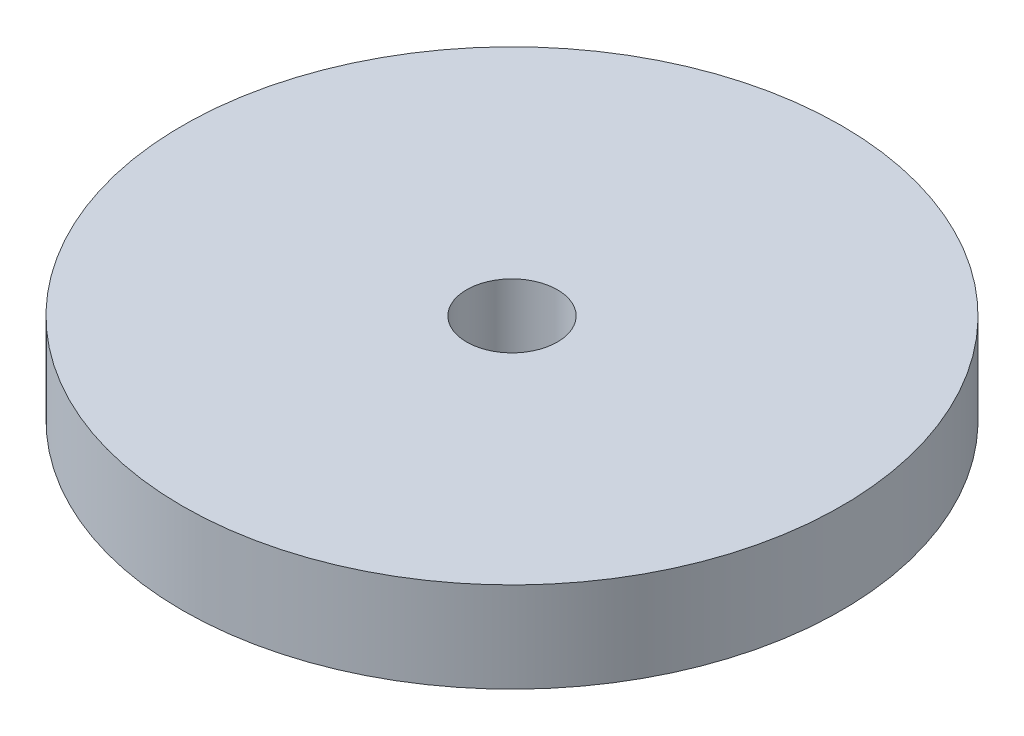
SolidWorks part; units mm, degrees
material "Delrin 2700 NC010, Low Viscosity Acetal Copolymer (SS)"
ref_plane "Front Plane" through (0, 0, 0) normal (0, 0, 1) x (1, 0, 0)
ref_plane "Top Plane" through (0, 0, 0) normal (0, 1, 0) x (1, 0, 0)
ref_plane "Right Plane" through (0, 0, 0) normal (1, 0, 0) x (0, 0, -1)
sketch "Sketch1" plane through (0, 0, 0) normal (0, 1, 0) x (1, 0, 0)
  circle A0 centre (0, 0) radius 18.542
  dimension "D1" = 37.084
extrude "Boss-Extrude1" add sketch "Sketch1" along normal blind 5.08
hole_wizard "1/4-20 Tapped Hole1" positions "Sketch3" profile "Sketch4" tap size "1/4-20" standard "ANSI Inch" end condition through all
sketch "Sketch3" plane through (0, 5.08, 0) normal (0, 1, 0) x (1, 0, 0)
  point P1 (0, 0)
sketch "Sketch4" plane through (0, 5.08, 0) normal (1, 0, 0) x (0, 0, 1)
  line L0 (0, 0) -> (0, 5.08)
  line L1 (0, 5.08) -> (2.5527, 5.08)
  line L2 (2.5527, 5.08) -> (2.5527, 0)
  line L5 (2.5527, 0) -> (0, 0)
  line L11 (0, -6.35) -> (0, 107.95) construction
  dimension "Thru Tap Drill Dia." = 5.1054
  dimension "Thru Tap Drill Depth" = 5.08
cosmetic thread "Hole Thread1" parameters "D2"=6.35
other "Move Face1" [suppressed] parameters "D1"=0.0508
